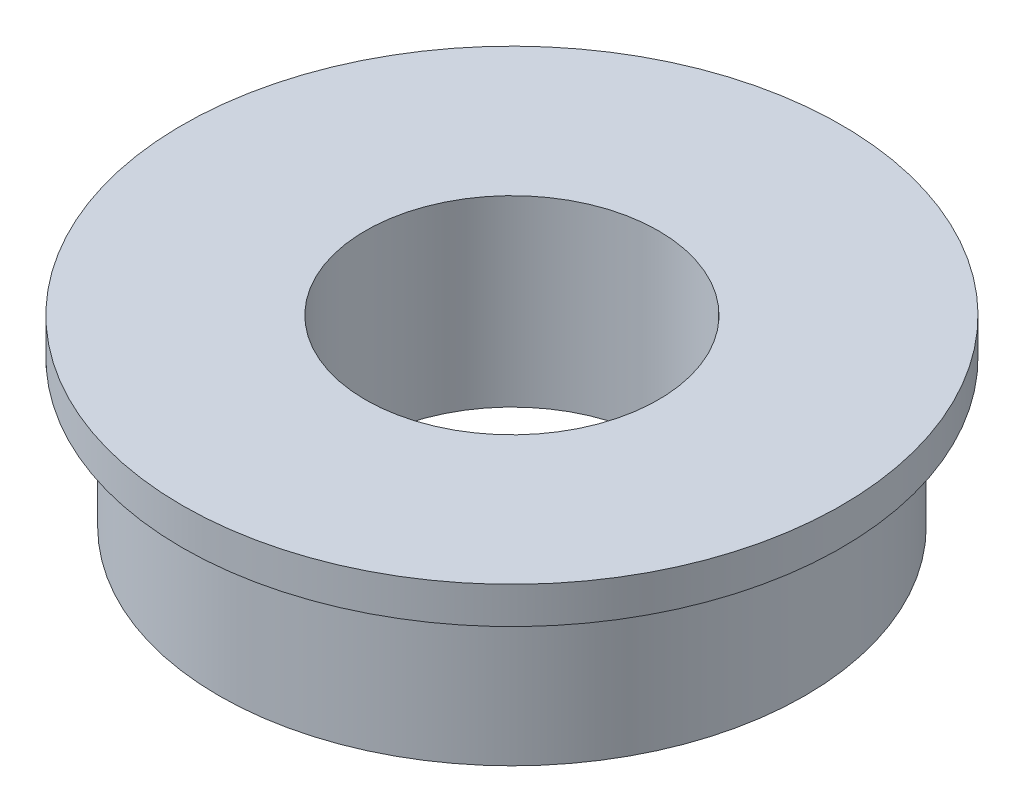
SolidWorks part; units mm, degrees
material "Cast Alloy Steel"
ref_plane "Front Plane" through (0, 0, 0) normal (0, 0, 1) x (1, 0, 0)
ref_plane "Top Plane" through (0, 0, 0) normal (0, 1, 0) x (1, 0, 0)
ref_plane "Right Plane" through (0, 0, 0) normal (1, 0, 0) x (0, 0, -1)
sketch "Sketch2" plane through (0, 0, 0) normal (0, 1, 0) x (1, 0, 0)
  circle A0 centre (0, 0) radius 8
  circle A1 centre (0, 0) radius 4
  dimension "D1" = 8
  dimension "D2" = 16
extrude "Boss-Extrude1" add sketch "Sketch2" along normal mid plane 5
sketch "Sketch3" plane through (0, 2.5, 0) normal (0, 1, 0) x (1, 0, 0)
  circle A0 centre (0, 0) radius 9
  circle A1 centre (0, 0) radius 8
  dimension "D1" = 18
extrude "Boss-Extrude3" add sketch "Sketch3" against normal blind 1 contours A0
sketch "Sketch5" plane through (0, -2.5, 0) normal (0, -1, 0) x (1, 0, 0)
  circle A0 centre (0, 0) radius 4
  circle A1 centre (0, 0) radius 4 construction
extrude "Cut-Extrude1" cut sketch "Sketch5" against normal through all
